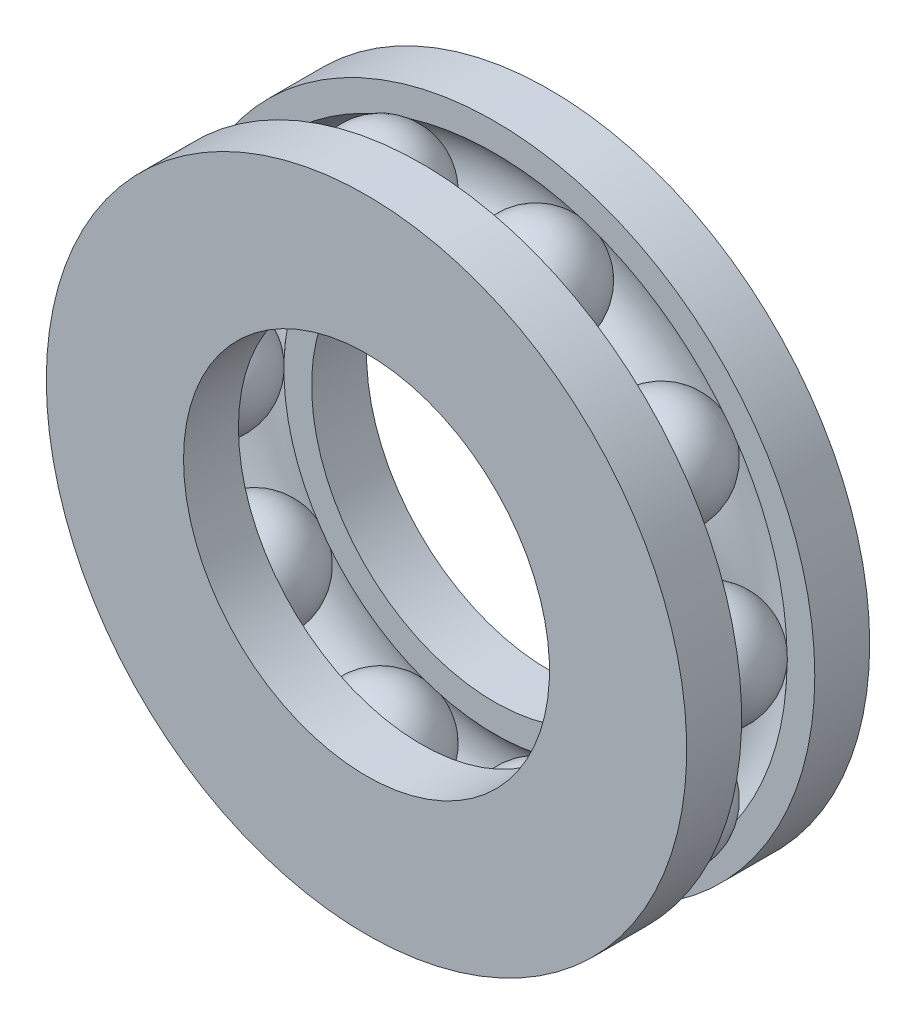
SolidWorks part; units mm, degrees
material "AISI 304"
ref_plane "Front Plane" through (0, 0, 0) normal (0, 0, 1) x (1, 0, 0)
ref_plane "Top Plane" through (0, 0, 0) normal (0, 1, 0) x (1, 0, 0)
ref_plane "Right Plane" through (0, 0, 0) normal (1, 0, 0) x (0, 0, -1)
sketch "Sketch1" plane through (0, 0, 0) normal (0, 0, 1) x (1, 0, 0)
  circle A0 centre (0, 0) radius 10
  circle A1 centre (0, 0) radius 17.5
  dimension "D1" = 35
  dimension "D2" = 20
extrude "Boss-Extrude1" add sketch "Sketch1" along normal blind 3
ref_plane "Plane1" through (0, 0, 10) normal (0, 0, -1) x (-1, 0, 0)
sketch "Sketch3" plane through (0, 0, 10) normal (0, 0, -1) x (-1, 0, 0)
  circle A0 centre (0, 0) radius 17.5 construction
  circle A1 centre (0, 0) radius 17.5
  circle A2 centre (0, 0) radius 10 construction
  circle A3 centre (0, 0) radius 10
extrude "Boss-Extrude2" add sketch "Sketch3" along normal blind 3 separate body
sketch "Sketch2" plane through (0, 0, 0) normal (0, 1, 0) x (1, 0, 0)
  line L0 (0, 0) -> (0, -12.3563) construction
  circle A0 centre (-13.75, -5) radius 3
  point P7 (0.2564, 0.152)
  dimension "D1" = 6
  dimension "D2" = 13.75
  dimension "D3" = 5
revolve "Cut-Revolve1" cut sketch "Sketch2" angle 360 about L0
sketch "Sketch4" plane through (0, 0, 0) normal (0, 1, 0) x (1, 0, 0)
  line L0 (-13.75, -9.6788) -> (-13.75, 0.293) construction
  line L1 (-13.75, -8.01) -> (-13.75, -1.99)
  arc A2 (-13.75, -1.99) -> (-13.75, -8.01) centre (-13.75, -5) ccw
  dimension "D1" = 3.01
revolve "Revolve1" add sketch "Sketch4" angle 360 about L0
pattern_circular "CirPattern6" count 10 every 36 about axis through (0, 0, 0) along (0, 0, 1) of "Revolve1"
